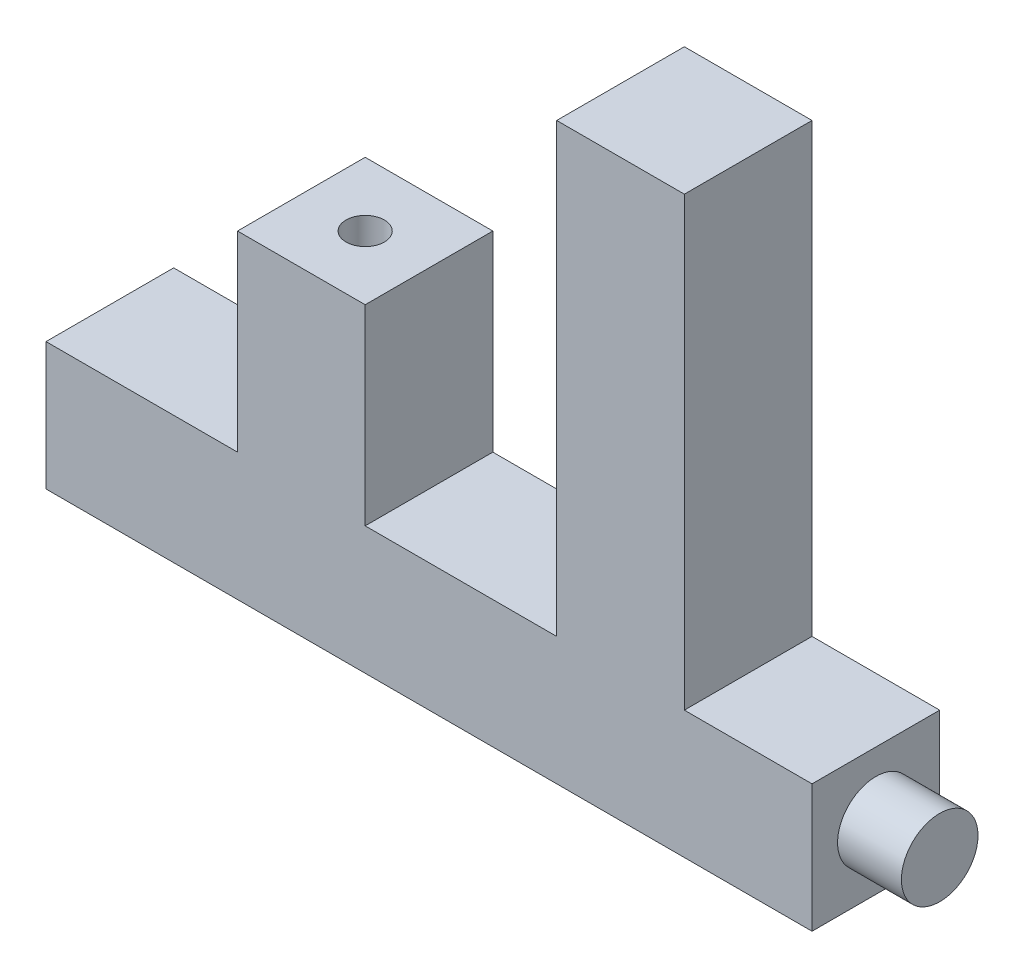
SolidWorks part; units mm, degrees
ref_plane "Front" through (0, 0, 0) normal (0, 0, 1) x (1, 0, 0)
ref_plane "Top" through (0, 0, 0) normal (0, 1, 0) x (1, 0, 0)
ref_plane "Right" through (0, 0, 0) normal (1, 0, 0) x (0, 0, -1)
sketch "Sketch1" plane through (0, 0, 0) normal (0, 0, 1) x (1, 0, 0)
  line L0 (30, 50) -> (50, 50)
  line L1 (50, 50) -> (50, 20)
  line L2 (50, 20) -> (80, 20)
  line L3 (80, 20) -> (80, 90)
  line L4 (80, 90) -> (100, 90)
  line L5 (100, 90) -> (100, 20)
  line L6 (100, 20) -> (130, 20)
  line L7 (0, 0) -> (0, 20)
  line L8 (0, 0) -> (130, 0)
  line L9 (130, 20) -> (130, 0)
  line L10 (30, 20) -> (30, 50)
  line L11 (0, 20) -> (30, 20)
  dimension "D1" = 20
  dimension "D2" = 20
  dimension "D3" = 30
  dimension "D4" = 70
  dimension "D5" = 30
  dimension "D6" = 130
  dimension "D8" = 30
extrude "Extrude1" add sketch "Sketch1" along normal blind 20
sketch "Sketch2" plane through (0, 50, 0) normal (0, 1, 0) x (-1, 0, 0)
  line L0 (-50, 0) -> (-30, 20) construction
  circle A0 centre (-40, 10) radius 3
  point P4 (-40, 10)
  point P11 (-40, 10)
  dimension "D1" = 6
extrude "Cut-Extrude2" cut sketch "Sketch2" against normal blind 10
sketch "Sketch3" plane through (130, 0, 0) normal (1, 0, 0) x (0, 0, -1)
  line L0 (-20, 0) -> (0, 20) construction
  circle A0 centre (-10, 10) radius 6
  point P4 (-10, 10)
extrude "Cut-Extrude3" cut sketch "Sketch3" against normal blind 10 flip side to cut
